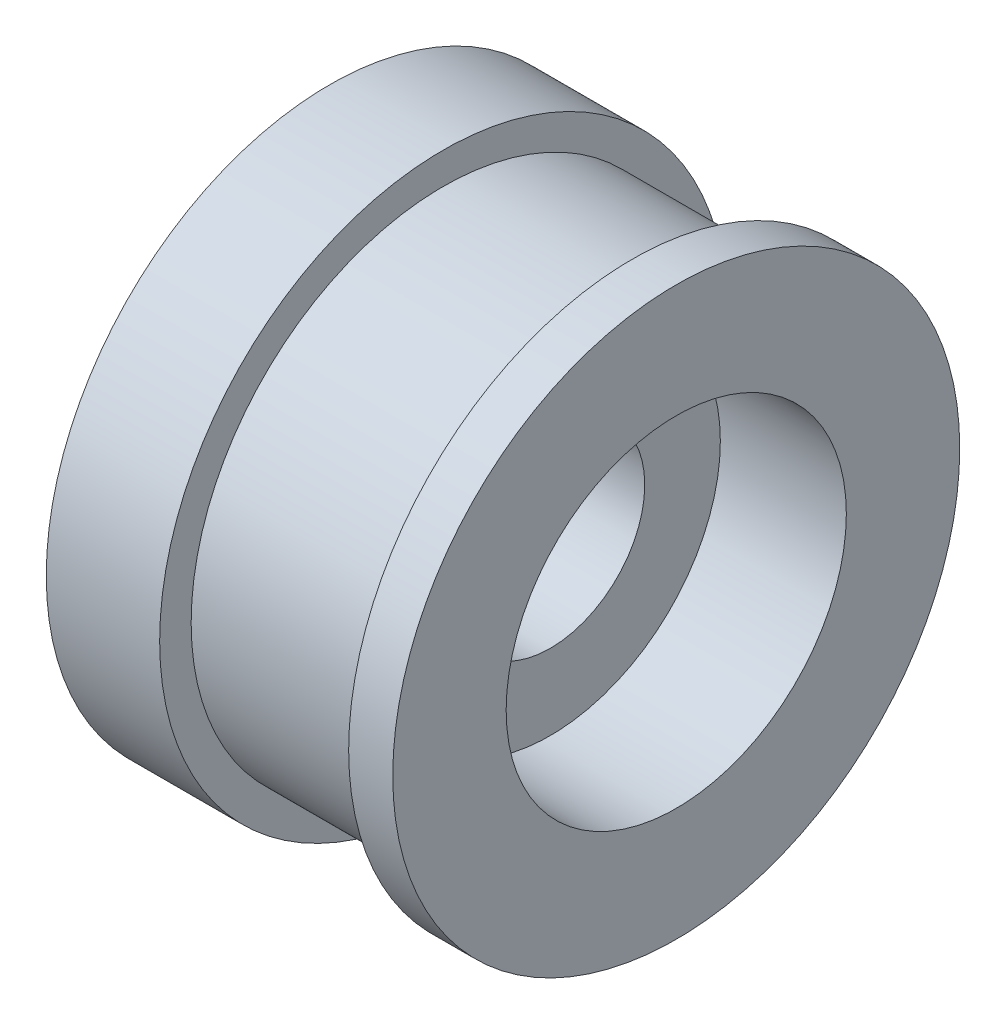
SolidWorks part; units mm, degrees
material "Custom Plastic"
ref_plane "Front Plane" through (0, 0, 0) normal (0, 0, 1) x (1, 0, 0)
ref_plane "Top Plane" through (0, 0, 0) normal (0, 1, 0) x (1, 0, 0)
ref_plane "Right Plane" through (0, 0, 0) normal (1, 0, 0) x (0, 0, -1)
sketch "Sketch1" plane through (0, 0, 0) normal (0, 1, 0) x (1, 0, 0)
  line L0 (-92.3358, 0) -> (112.6048, 0) construction
  line L1 (0, 0) -> (0, 4.5)
  line L2 (0, 4.5) -> (1.8, 4.5)
  line L3 (1.8, 4) -> (1.8, 4.5)
  line L4 (5.5, 0) -> (5.5, 4.5)
  line L5 (5.5, 4.5) -> (4.8, 4.5)
  line L6 (4.8, 4.5) -> (4.8, 4)
  line L7 (1.8, 4) -> (4.8, 4)
  line L8 (0, 0) -> (5.5, 0)
  dimension "D1" = 4.5
  dimension "D2" = 1.8
  dimension "D3" = 0.5
  dimension "D4" = 5.5
  dimension "D5" = 4.5
  dimension "D6" = 0.7
revolve "Revolve1" add sketch "Sketch1" angle 360 about L0
sketch "Sketch2" plane through (0, 0, 0) normal (-1, 0, 0) x (0, 0, 1)
  circle A0 centre (0, 0) radius 1.5
  dimension "D1" = 3
extrude "Cut-Extrude1" cut sketch "Sketch2" against normal blind 10
sketch "Sketch3" plane through (5.5, 0, 0) normal (1, 0, 0) x (0, 0, -1)
  circle A0 centre (0, 0) radius 2.7
  dimension "D1" = 5.4
extrude "Cut-Extrude2" cut sketch "Sketch3" against normal blind 2
